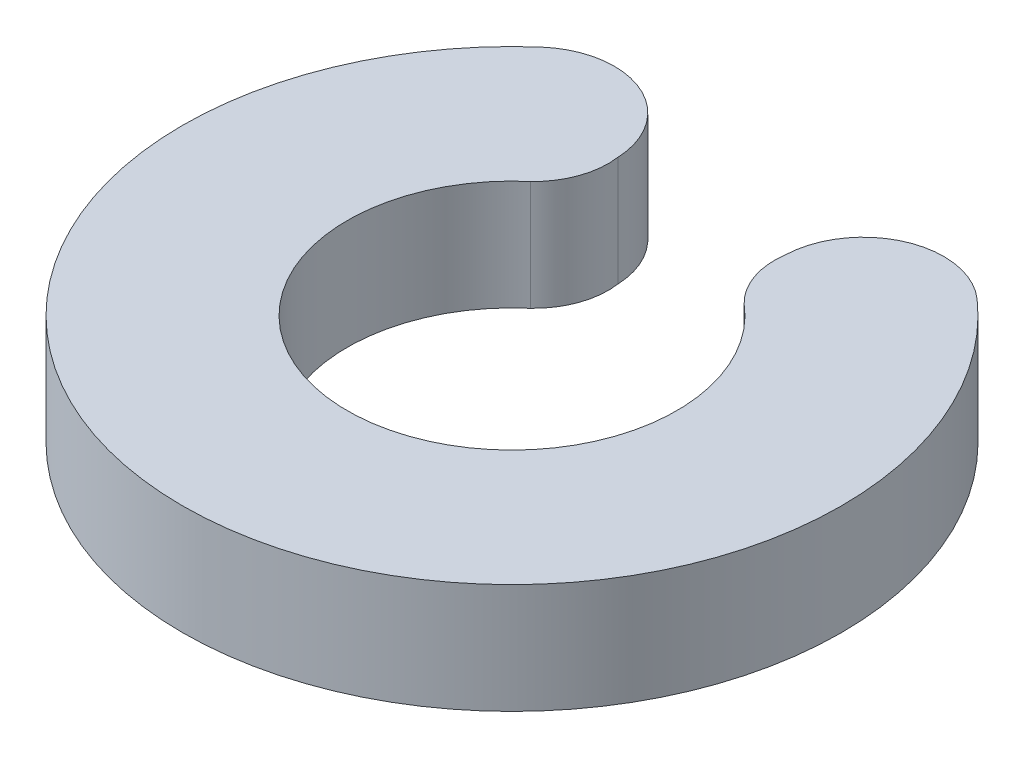
SolidWorks part; units mm, degrees
ref_plane "Front Plane" through (0, 0, 0) normal (0, 0, 1) x (1, 0, 0)
ref_plane "Top Plane" through (0, 0, 0) normal (0, 1, 0) x (1, 0, 0)
ref_plane "Right Plane" through (0, 0, 0) normal (1, 0, 0) x (0, 0, -1)
sketch "Sketch1" plane through (0, 0, 0) normal (0, 1, 0) x (1, 0, 0)
  line L1 (-3, 0) -> (3, 0)
  arc A0 (-1.9453, 2.2838) -> (1.933, 2.2943) centre (0, 0) ccw
  arc A1 (-3.9729, 4.4962) -> (3.9729, 4.4962) centre (0, 0) ccw
  arc A2 (-1.532, 3.4577) -> (-3.9729, 4.4962) centre (-3, 3.3951) ccw
  arc A3 (3.9729, 4.4962) -> (1.532, 3.4577) centre (3, 3.3951) ccw
  arc A4 (-2.0188, 2.2191) -> (-1.532, 3.4577) centre (-2.8816, 3.2732) ccw
  arc A5 (2.0188, 2.2191) -> (1.532, 3.4577) centre (2.8577, 3.2638) cw
  point P1 (1.6107, 2.7737)
  point P5 (-1.6138, 2.7749)
  dimension "D1" = 6
  dimension "D2" = 12
  dimension "D3" = 1.4694
  dimension "D4" = 1.4694
  dimension "D5" = 3
  dimension "D6" = 3
  dimension "D9" = 1.3621
  dimension "D11" = 5.7392
  dimension "D7" = 1.6107
  dimension "D8" = 1.3398
  dimension "D10" = 2.8816
  dimension "D12" = 1.6138
extrude "Boss-Extrude1" add sketch "Sketch1" along normal blind 2 contours A5 A0 A4 A2 A1 A3
